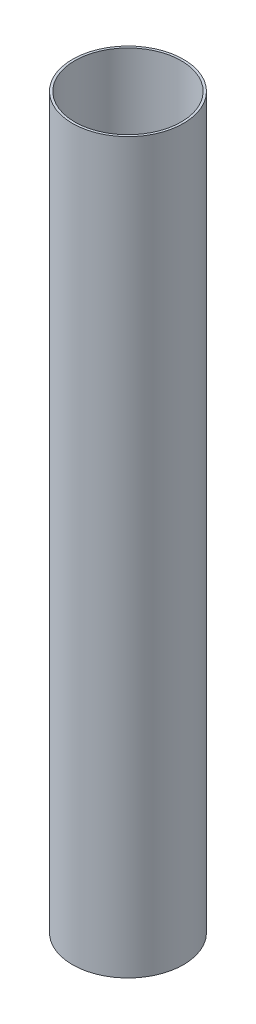
SolidWorks part; units mm, degrees
ref_plane "Front Plane" through (0, 0, 0) normal (0, 0, 1) x (1, 0, 0)
ref_plane "Top Plane" through (0, 0, 0) normal (0, 1, 0) x (1, 0, 0)
ref_plane "Right Plane" through (0, 0, 0) normal (1, 0, 0) x (0, 0, -1)
sketch "Sketch1" plane through (0, 0, 0) normal (0, 1, 0) x (1, 0, 0)
  circle A0 centre (0, 0) radius 38.1
  circle A1 centre (0, 0) radius 36.5
  dimension "D1" = 76.2
  dimension "D2" = 1.6
extrude "Boss-Extrude1" add sketch "Sketch1" along normal blind 500
